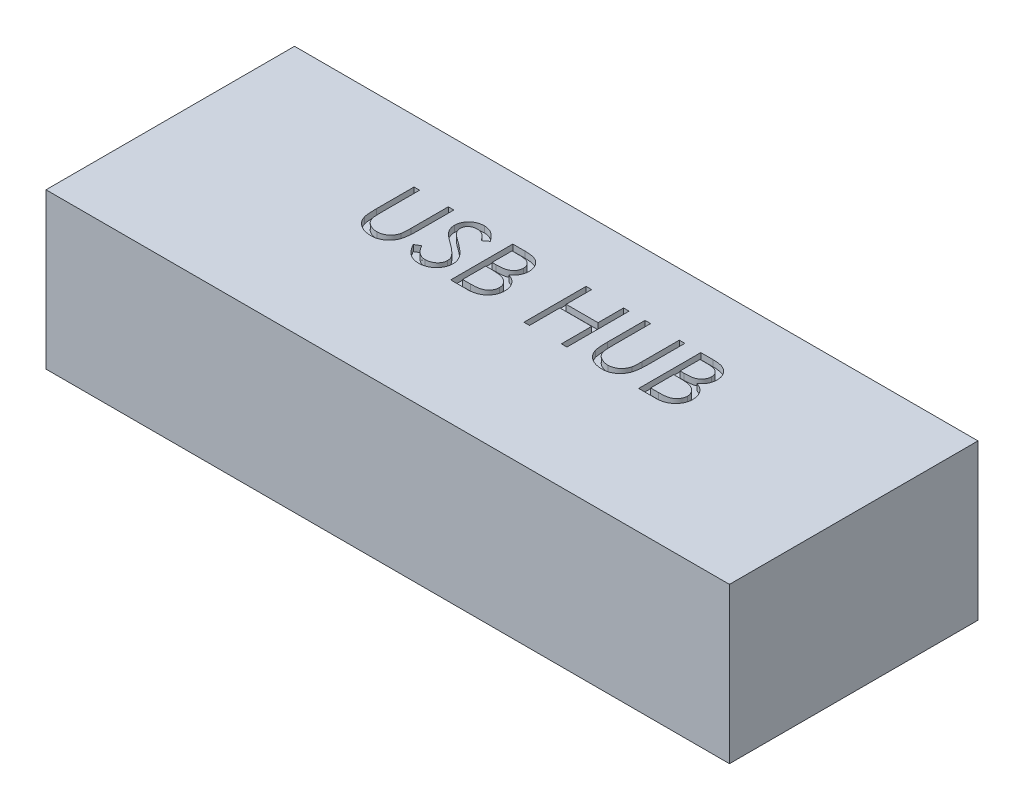
SolidWorks part; units mm, degrees
ref_plane "Front Plane" through (0, 0, 0) normal (0, 0, 1) x (1, 0, 0)
ref_plane "Top Plane" through (0, 0, 0) normal (0, 1, 0) x (1, 0, 0)
ref_plane "Right Plane" through (0, 0, 0) normal (1, 0, 0) x (0, 0, -1)
sketch "Sketch1" plane through (0, 0, 0) normal (0, 1, 0) x (1, 0, 0)
  line L1 (0, 0) -> (110, 0)
  line L2 (0, 0) -> (0, 40)
  line L3 (0, 40) -> (110, 40)
  line L4 (110, 0) -> (110, 40)
  dimension "D1" = 110
  dimension "D2" = 40
extrude "Boss-Extrude1" add sketch "Sketch1" along normal blind 25
sketch "Sketch2" plane through (0, 25, 0) normal (0, 1, 0) x (1, 0, 0)
  line L0 (0, 20) -> (110, 20) construction
  line L1 (0, 40) -> (0, 0) construction
  line L2 (110, 0) -> (110, 40) construction
  text T0 "USB HUB" font "Century Gothic" height 10
extrude "Cut-Extrude1" cut sketch "Sketch2" against normal blind 1
